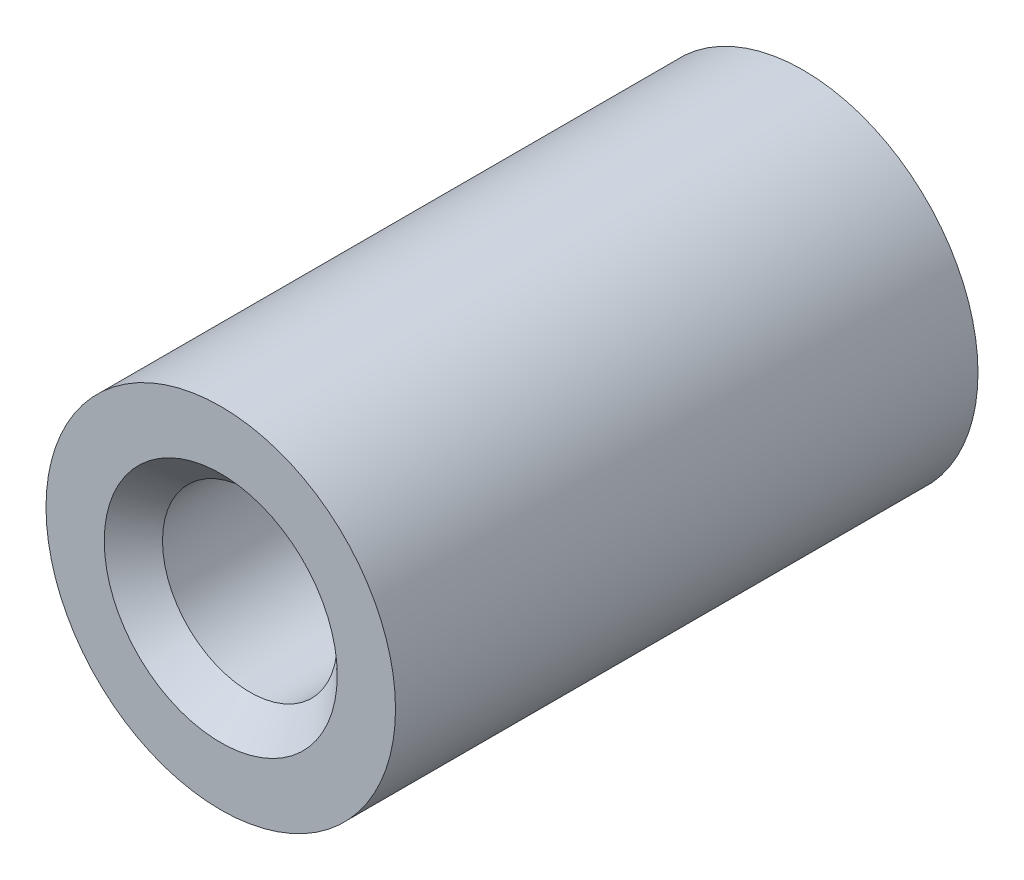
SolidWorks part; units mm, degrees
ref_plane "Piano frontale" through (0, 0, 0) normal (0, 0, 1) x (1, 0, 0)
ref_plane "Piano superiore" through (0, 0, 0) normal (0, 1, 0) x (1, 0, 0)
ref_plane "Piano destro" through (0, 0, 0) normal (1, 0, 0) x (0, 0, -1)
sketch "Schizzo1" plane through (0, 0, 0) normal (0, 0, 1) x (1, 0, 0)
  circle A0 centre (0, 0) radius 3
  circle A1 centre (0, 0) radius 1.5
  dimension "D1" = 3
  dimension "D2" = 6
extrude "Estrusione-Estrusione1" add sketch "Schizzo1" along normal blind 10
chamfer "Smusso1" distance 0.5 angle 45 1 edges at (1.5, 0, 10)
chamfer "Chamfer1" distance 0.5 angle 45 1 edges at (1.5, 0, 0)
